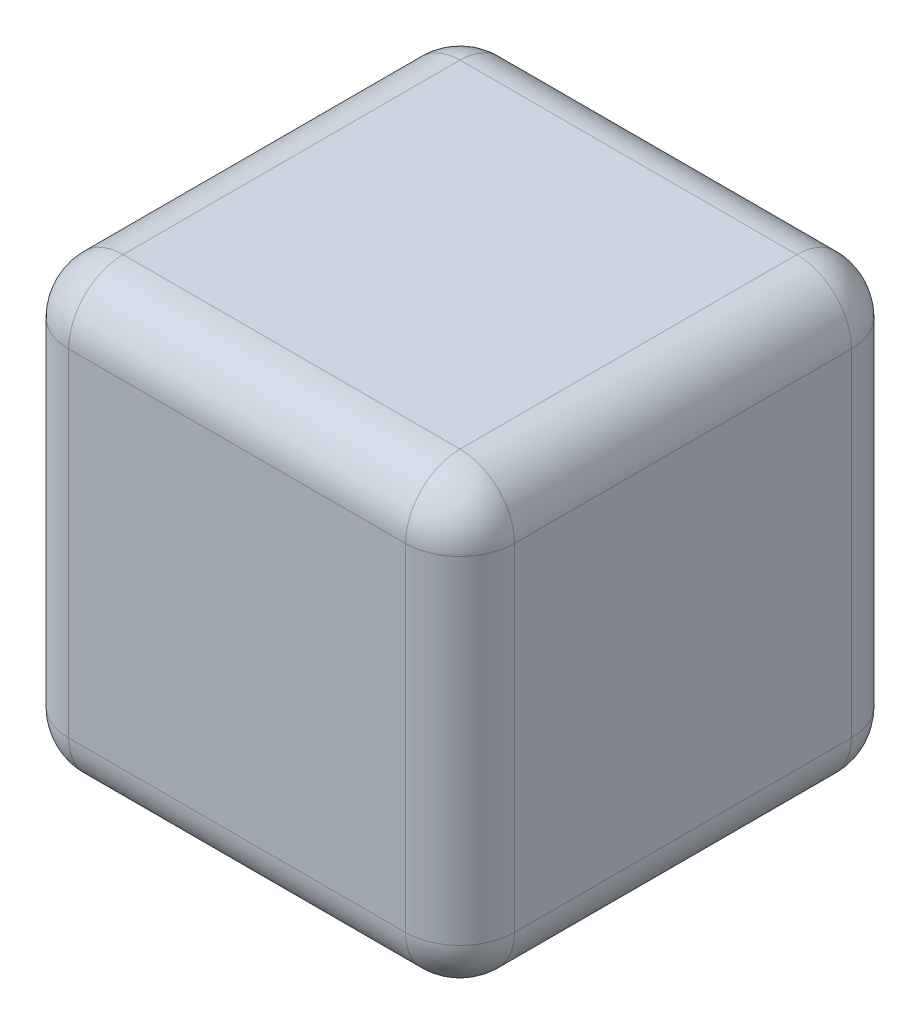
SolidWorks part; units mm, degrees
ref_plane "Front Plane" through (0, 0, 0) normal (0, 0, 1) x (1, 0, 0)
ref_plane "Top Plane" through (0, 0, 0) normal (0, 1, 0) x (1, 0, 0)
ref_plane "Right Plane" through (0, 0, 0) normal (1, 0, 0) x (0, 0, -1)
sketch "Sketch1" plane through (0, 0, 0) normal (0, 1, 0) x (1, 0, 0)
  line L1 (-45, 45) -> (45, 45)
  line L2 (-45, 45) -> (-45, -45)
  line L3 (-45, -45) -> (45, -45)
  line L4 (45, 45) -> (45, -45)
  line L5 (-45, 45) -> (45, -45) construction
  line L6 (-45, -45) -> (45, 45) construction
  point P0 (0, 0)
  dimension "D1" = 90
  dimension "D2" = 90
extrude "Boss-Extrude1" add sketch "Sketch1" along normal blind 90
fillet "Fillet1" radius 11 12 edges at (0, 90, 45) (0, 0, 45) (0, 90, -45) (0, 0, -45) (-45, 45, -45) (-45, 90, 0) (-45, 45, 45) (-45, 0, 0) (45, 45, 45) (45, 90, 0) (45, 45, -45) (45, 0, 0)
